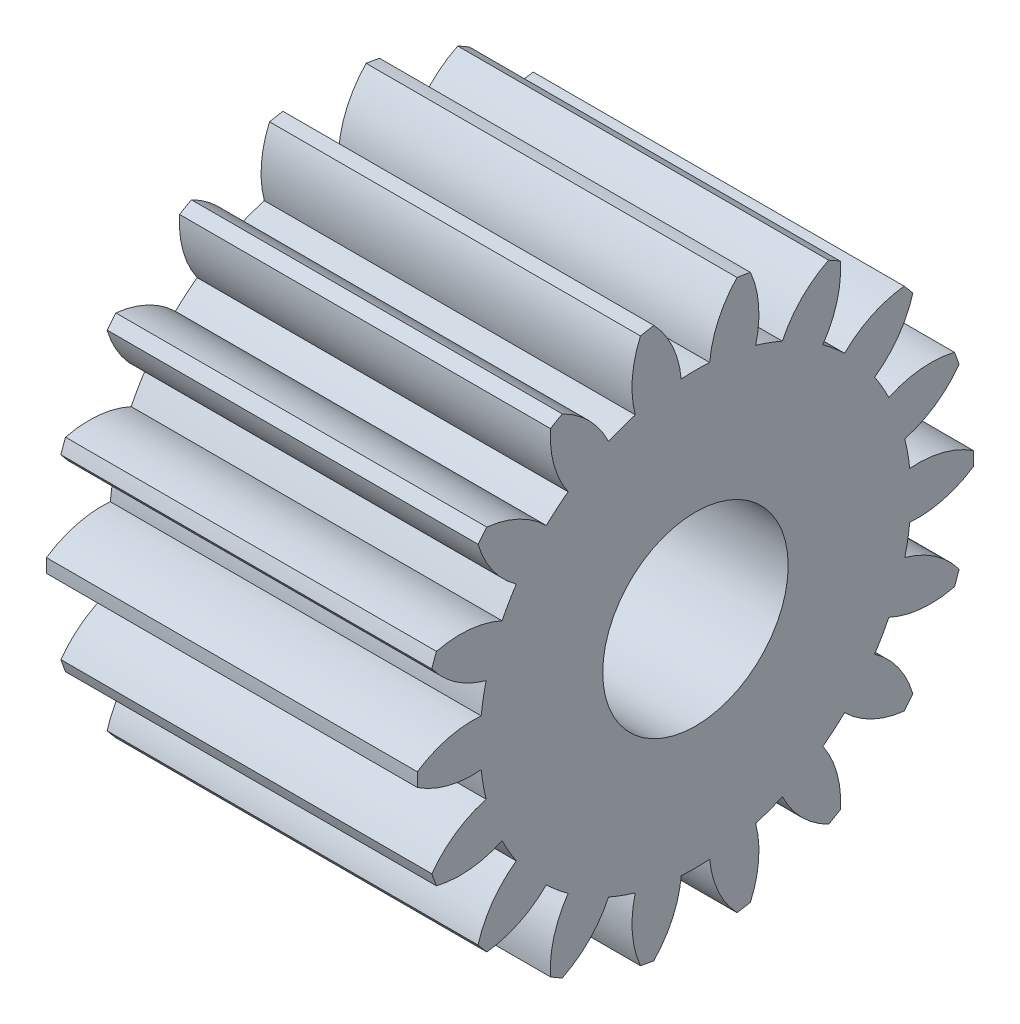
SolidWorks part; units mm, degrees
ref_plane "Plane1" through (0, 0, 0) normal (0, 0, 1) x (1, 0, 0)
ref_plane "Plane2" through (0, 0, 0) normal (0, 1, 0) x (1, 0, 0)
ref_plane "Plane3" through (0, 0, 0) normal (1, 0, 0) x (0, 0, -1)
other "Configuration Table"
sketch "HoldingSke" plane through (0, 0, 0) normal (0, 1, 0) x (1, 0, 0)
  line L0 (0, 0) -> (1.5851, -0.515)
  line L1 (-15, 0) -> (100, 0) construction
  line L2 (0, 0) -> (-2.1039, 2.3779)
  line L3 (0, 0) -> (-11.863, 4.5341)
  line L4 (0, 0) -> (8.2133, 2.6687)
  line L5 (0, 0) -> (-46.8476, -17.4728)
  line L6 (0, 0) -> (-6.6317, -4.4744)
  line L7 (-2.1039, 2.3779) -> (8.6586, 51.2059)
  line L8 (-76.2, 54.61) -> (-76.1, 54.61)
  line L9 (-71.009, 38.7566) -> (-53.1078, 45.2721)
  line L10 (-76.2, 71.12) -> (104.1128, 71.12)
  line L11 (0, 0) -> (-8, 0)
  line L12 (-76.2, 101.6) -> (-76.177, 101.6)
  line L13 (24.9733, 27.94) -> (52.9518, 28.4284)
  line L14 (24.9733, 27.94) -> (24.9743, 27.94)
  line L15 (24.9733, 27.94) -> (100.4006, 29.5858)
  line L16 (-63.627, -0.6) -> (-12.827, -0.6)
  circle A0 centre (0, 0) radius 0.5
  circle A1 centre (0, 0) radius 4.649
  circle A2 centre (0, 0) radius 37.5
  circle A3 centre (0, 0) radius 0.5
  dimension "MHD" = 9.298
  dimension "Hub_dia" = 75
  dimension "Bore" = 1
  dimension "MBD" = 1
  dimension "Num_teeth" = 18
  dimension "Pitch" = 1.6667
  dimension "Overall_len" = 50
  dimension "Show_teeth" = 18
  dimension "Thickness" = 8
  dimension "OAL" = 50.0001
  dimension "T_dim" = 0.1
  dimension "Ap" = 20
  dimension "H" = 19.05
  dimension "Pitch_radius" = 180.3128
  dimension "Width" = 8
  dimension "Backlash" = 0.023
  dimension "Addendum_fac" = 1
  dimension "Dedendum_fac" = 1.25
  dimension "Clearance_fac" = 0.25
  dimension "Dedendum_add" = 0.001
  dimension "Module" = 0.6
sketch "BasProSke" plane through (0, 0, 0) normal (0, 1, 0) x (1, 0, 0)
  line L0 (-10, 0) -> (60, 0) construction
  line L1 (0, 0) -> (0, 6)
  line L2 (0, 0) -> (8, 0)
  line L3 (8, 0) -> (8, 6)
  line L4 (8, 6) -> (0, 6)
  dimension "Thickness" = 8
  dimension "Diameter" = 12
revolve "Base-Revolve" add sketch "BasProSke" angle 360 about L0
sketch "TooCutSke" plane through (0, 0, 0) normal (1, 0, 0) x (0, 0, -1)
  line L1 (0, 0) -> (0, 107) construction
  line L2 (0, 0) -> (-0.5109, 5.3758) construction
  line L3 (0, 0) -> (-1.8694, 10.6021) construction
  line L4 (-0.5109, 5.3758) -> (-0.9347, 5.301) construction
  arc A0 (0.3066, 4.6389) -> (-0.3066, 4.6389) centre (0, 0) ccw
  arc A1 (0.9183, 5.955) -> (-0.9183, 5.955) centre (0, 0) ccw
  circle A2 centre (0, 0) radius 5.4 construction
  circle A3 centre (0, 0) radius 5.0743 construction
  arc A4 (-0.3066, 4.6389) -> (-0.9183, 5.955) centre (-2.4574, 4.4396) ccw
  arc A5 (0.9183, 5.955) -> (0.3066, 4.6389) centre (2.4574, 4.4396) ccw
  dimension "Root_dia" = 9.298
  dimension "Overcut_dia" = 12.0508
  dimension "Pitch_dia" = 10.8
  dimension "Base_dia" = 10.1487
  dimension "Flank_rad" = 2.16
  dimension "Half_ang" = 10
  dimension "Half_CT" = 0.4304
extrude "ToothCut" cut sketch "TooCutSke" along normal through all
fillet "Breaks" [suppressed] radius 0.012
fillet "RootFillets" [suppressed] radius 0.151
pattern_circular "TeethCuts" count 18 every 20 about axis through (-10, 0, 0) along (1, 0, 0) of "ToothCut", "RootFillets", "Breaks"
sketch "HubNeaOneSke" plane through (0, 0, 0) normal (-1, 0, 0) x (0, 0, 1)
  circle A0 centre (0, 0) radius 4.649
  dimension "Diameter" = 9.298
extrude "HubNearOne" [suppressed] add sketch "HubNeaOneSke" along normal blind 42.0001
sketch "HubNeaBotSke" plane through (0, 0, 0) normal (-1, 0, 0) x (0, 0, 1)
  circle A0 centre (0, 0) radius 4.649
  dimension "Diameter" = 9.298
extrude "HubNearBoth" [suppressed] add sketch "HubNeaBotSke" along normal blind 21
ref_plane "FarPln" through (8, 0, 0) normal (1, 0, 0) x (0, 0, -1)
sketch "HubFarSke" plane through (8, 0, 0) normal (1, 0, 0) x (0, 0, -1)
  circle A0 centre (0, 0) radius 4.649
  dimension "Diameter" = 9.298
extrude "HubFar" [suppressed] add sketch "HubFarSke" along normal blind 21
sketch "BorSke" plane through (0, 0, 0) normal (1, 0, 0) x (0, 0, -1)
  circle A0 centre (0, 0) radius 0.5
  dimension "Diameter" = 1
extrude "Bore" cut sketch "BorSke" along normal mid plane 100.0001
sketch "KeySke" plane through (0, 0, 0) normal (1, 0, 0) x (0, 0, -1)
  line L0 (-0.05, 0) -> (-0.05, 0.6)
  line L1 (-0.05, 0.6) -> (0.05, 0.6)
  line L2 (0.05, 0.6) -> (0.05, 0)
  line L3 (0, 0) -> (0, 34) construction
  line L4 (-0.05, 0) -> (0.05, 0)
  dimension "Offset" = 0.6
  dimension "Width" = 0.1
extrude "Keyway" [suppressed] cut sketch "KeySke" along normal mid plane 100.0001
pattern_circular "Keyway2" [suppressed] count 2 every 90 about axis through (-10, 0, 0) along (1, 0, 0)
sketch "Sketch1" plane through (8, 0, 0) normal (1, 0, 0) x (0, 0, -1)
  circle A0 centre (0, 0) radius 2
  dimension "D1" = 4
extrude "Cut-Extrude1" cut sketch "Sketch1" against normal through all
equation "' \"Module@HoldingSke\" = 6.35"
equation "' \"Num_teeth@HoldingSke\" = 12"
equation "' \"Ap@HoldingSke\" =  20"
equation "' \"Ap@HoldingSke\" = 20"
equation "' \"Width@HoldingSke\" = 0.5 * 25.4"
equation "' \"Hub_dia@HoldingSke\"= 1 * 25.4"
equation "' \"Hub_dia@HoldingSke\" = 1 * 25.4"
equation "' \"Overall_len@HoldingSke\" = 1.0 * 25.4"
equation "' \"Bore@HoldingSke\" = 0.75 * 25.4"
equation "' \"T_dim@HoldingSke\" = 0.1 * 25.4"
equation "' \"Width@KeySke\" = 0.25 * 25.4"
equation "' \"Show_teeth@HoldingSke\" = 13"
equation "' \"Backlash@HoldingSke\" = 0.009 * 25.4"
equation "' \"Addendum_fac@HoldingSke\" = 1.0"
equation "' \"Dedendum_fac@HoldingSke\" = 1.25"
equation "' \"Dedendum_add@HoldingSke\" = 0.00005 * 25.4"
equation "' \"Clearance_fac@HoldingSke\" = 0.25"
equation "\"Pitch@HoldingSke\" = 1 / \"Module@HoldingSke\""
equation "\"Overcut_dia@TooCutSke\" = (\"Num_teeth@HoldingSke\" + 2 * \"Addendum_fac@HoldingSke\") / \"Pitch@HoldingSke\" + 0.002 * 25.4"
equation "\"Pitch_dia@TooCutSke\" = \"Num_teeth@HoldingSke\" / \"Pitch@HoldingSke\""
equation "\"Base_dia@TooCutSke\" = \"Num_teeth@HoldingSke\" / \"Pitch@HoldingSke\" * cos((\"Ap@HoldingSke\"  * 3.14159265 / 180))"
equation "\"Root_dia@TooCutSke\" = (\"Num_teeth@HoldingSke\" + 2) / \"Pitch@HoldingSke\" - 2 * (\"Addendum_fac@HoldingSke\" + \"Dedendum_fac@HoldingSke\") / \"Pitch@HoldingSke\" - \"Dedendum_add@HoldingSke\" * 2"
equation "\"Half_ang@TooCutSke\" = 180 / \"Num_teeth@HoldingSke\""
equation "\"Half_CT@TooCutSke\" = \"Num_teeth@HoldingSke\" / \"Pitch@HoldingSke\" * sin((3.14159265 / 2 / \"Num_teeth@HoldingSke\")) / 2 - 7 * \"Backlash@HoldingSke\" / 4"
equation "\"Flank_rad@TooCutSke\" = \"Num_teeth@HoldingSke\" / \"Pitch@HoldingSke\" / 5"
equation "\"Radius@RootFillets\" = \"Clearance_fac@HoldingSke\" / \"Pitch@HoldingSke\" + \"Dedendum_add@HoldingSke\""
equation "\"Break_rad@Breaks\" = 0.02 / \"Pitch@HoldingSke\""
equation "\"Thickness@HoldingSke\" = \"Width@HoldingSke\""
equation "\"OAL@HoldingSke\" = \"Thickness@HoldingSke\""
equation "\"MHD@HoldingSke\" = (\"Num_teeth@HoldingSke\" + 2) / \"Pitch@HoldingSke\" - 2 * (\"Addendum_fac@HoldingSke\" + \"Dedendum_fac@HoldingSke\")  / \"Pitch@HoldingSke\" - \"Dedendum_add@HoldingSke\" * 2"
equation "\"MBD@HoldingSke\" = (\"Num_teeth@HoldingSke\" + 2) / \"Pitch@HoldingSke\" - 2 * (\"Addendum_fac@HoldingSke\" + \"Dedendum_fac@HoldingSke\")  / \"Pitch@HoldingSke\" - \"Dedendum_add@HoldingSke\" * 2 - 0.002 * 25.4"
equation "\"MHD@HoldingSke\" = ((sgn( \"MHD@HoldingSke\" - \"Hub_dia@HoldingSke\" )-1)*( \"MHD@HoldingSke\" - \"Hub_dia@HoldingSke\" ))/-2+ \"Hub_dia@HoldingSke\""
equation "\"MBD@HoldingSke\" = ((sgn( \"MBD@HoldingSke\" - \"Bore@HoldingSke\" )-1)*( \"MBD@HoldingSke\" - \"Bore@HoldingSke\" ))/-2+ \"Bore@HoldingSke\""
equation "\"OAL@HoldingSke\" = ((sgn( \"OAL@HoldingSke\" - \"Overall_len@HoldingSke\" )+1)*( \"OAL@HoldingSke\" - \"Overall_len@HoldingSke\" ))/2 + \"Overall_len@HoldingSke\" + 0.000002 * 25.4"
equation "\"Num_teeth@TeethCuts\" = int( \"Show_teeth@HoldingSke\" ) + 1"
equation "\"Num_teeth@TeethCuts\" = ((sgn( \"Num_teeth@TeethCuts\" - \"Num_teeth@HoldingSke\" )-1)*( \"Num_teeth@TeethCuts\" - \"Num_teeth@HoldingSke\" ))/-2+ \"Num_teeth@HoldingSke\""
equation "\"Num_teeth@TeethCuts\" = ((sgn( \"Num_teeth@TeethCuts\" - 2.0)+1)*( \"Num_teeth@TeethCuts\" - 2.0))/2 +2.0"
equation "\"Angle@TeethCuts\" = 360.0 / \"Num_teeth@HoldingSke\""
equation "\"Diameter@BasProSke\" = (\"Num_teeth@HoldingSke\" + 2 * \"Addendum_fac@HoldingSke\") / \"Pitch@HoldingSke\""
equation "\"Thickness@BasProSke\"  = \"Thickness@HoldingSke\""
equation "' \"Fillet_rad@BasProSke\" =  \"Thickness@HoldingSke\" * 0.05"
equation "' \"Fillet_rad@BasProSke\" = \"Thickness@HoldingSke\" * 0.05"
equation "\"MHD@HoldingSke\" = ((sgn( \"MHD@HoldingSke\" - \"Root_dia@TooCutSke\" )-1)*( \"MHD@HoldingSke\" - \"Root_dia@TooCutSke\" ))/-2+ \"Root_dia@TooCutSke\""
equation "\"Diameter@HubNeaOneSke\" = \"MHD@HoldingSke\""
equation "\"Length@HubNearOne\" = \"OAL@HoldingSke\" - \"Thickness@BasProSke\""
equation "\"Diameter@HubNeaBotSke\" = \"MHD@HoldingSke\""
equation "\"Length@HubNearBoth\" = ( \"OAL@HoldingSke\" - \"Thickness@BasProSke\" ) / 2.0"
equation "\"Thickness@FarPln\" = \"Thickness@BasProSke\""
equation "\"Diameter@HubFarSke\" = \"MHD@HoldingSke\""
equation "\"Length@HubFar\" = ( \"OAL@HoldingSke\" - \"Thickness@BasProSke\" ) / 2.0"
equation "\"Diameter@BorSke\" = \"MBD@HoldingSke\""
equation "\"D1@Bore\" = \"OAL@HoldingSke\" * 2.0"
equation "\"D1@Keyway\" = \"OAL@HoldingSke\" * 2.0"
equation "\"Offset@KeySke\" = \"T_dim@HoldingSke\" + \"MBD@HoldingSke\" / 2.0"
